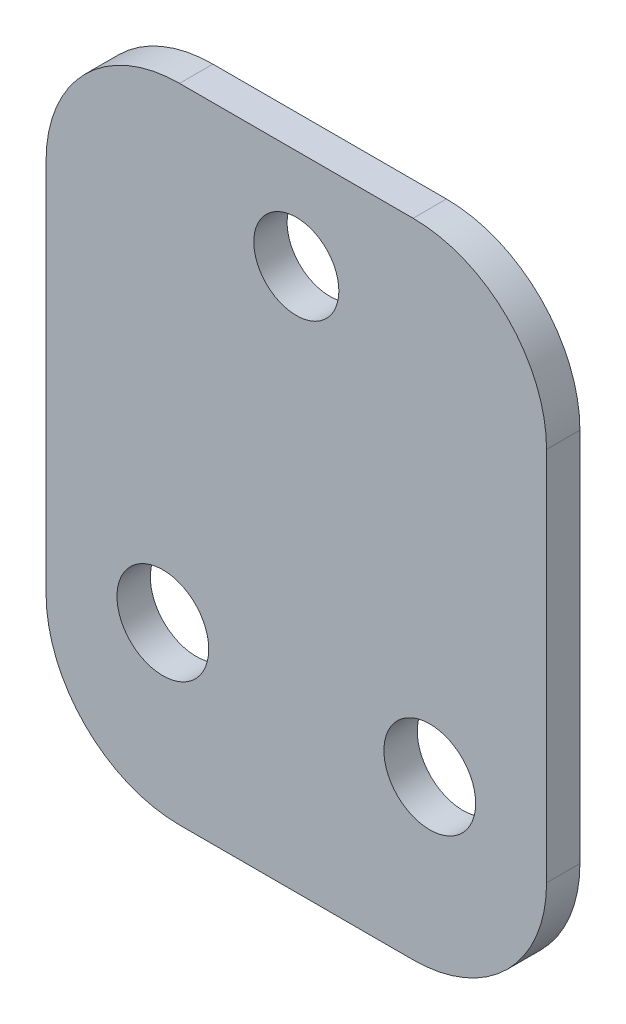
SolidWorks part; units mm, degrees
material "Plain Carbon Steel"
ref_plane "Front Plane" through (0, 0, 0) normal (0, 0, 1) x (1, 0, 0)
ref_plane "Top Plane" through (0, 0, 0) normal (0, 1, 0) x (1, 0, 0)
ref_plane "Right Plane" through (0, 0, 0) normal (1, 0, 0) x (0, 0, -1)
sketch "Sketch1" plane through (0, 0, 0) normal (0, 0, 1) x (1, 0, 0)
  line L0 (-8, -10) -> (0, -10) construction
  line L1 (-15, -20) -> (15, -20)
  line L2 (-15, -20) -> (-15, 18.5)
  line L3 (-15, 18.5) -> (15, 18.5)
  line L4 (15, -20) -> (15, 18.5)
  line L5 (-15, -20) -> (15, 18.5) construction
  line L6 (-15, 18.5) -> (15, -20) construction
  line L7 (0, -10) -> (8, -10) construction
  line L8 (0, -10) -> (0, -0.75) construction
  line L9 (0, -10) -> (0, -20) construction
  line L10 (0, -0.75) -> (0, 12.5) construction
  circle A0 centre (0, 12.5) radius 2.55
  circle A1 centre (-8, -10) radius 2.75
  circle A2 centre (8, -10) radius 2.75
  point P0 (0, 0)
  dimension "D7" = 5.5
  dimension "D8" = 5.1
  dimension "D1" = 12.5
  dimension "D2" = 10
  dimension "D3" = 10
  dimension "D4" = 8
  dimension "D5" = 7
  dimension "D6" = 6
extrude "Boss-Extrude1" add sketch "Sketch1" along normal blind 2
fillet "Fillet1" radius 8 4 edges at (15, -20, 1) (-15, -20, 1) (15, 18.5, 1) (-15, 18.5, 1)
